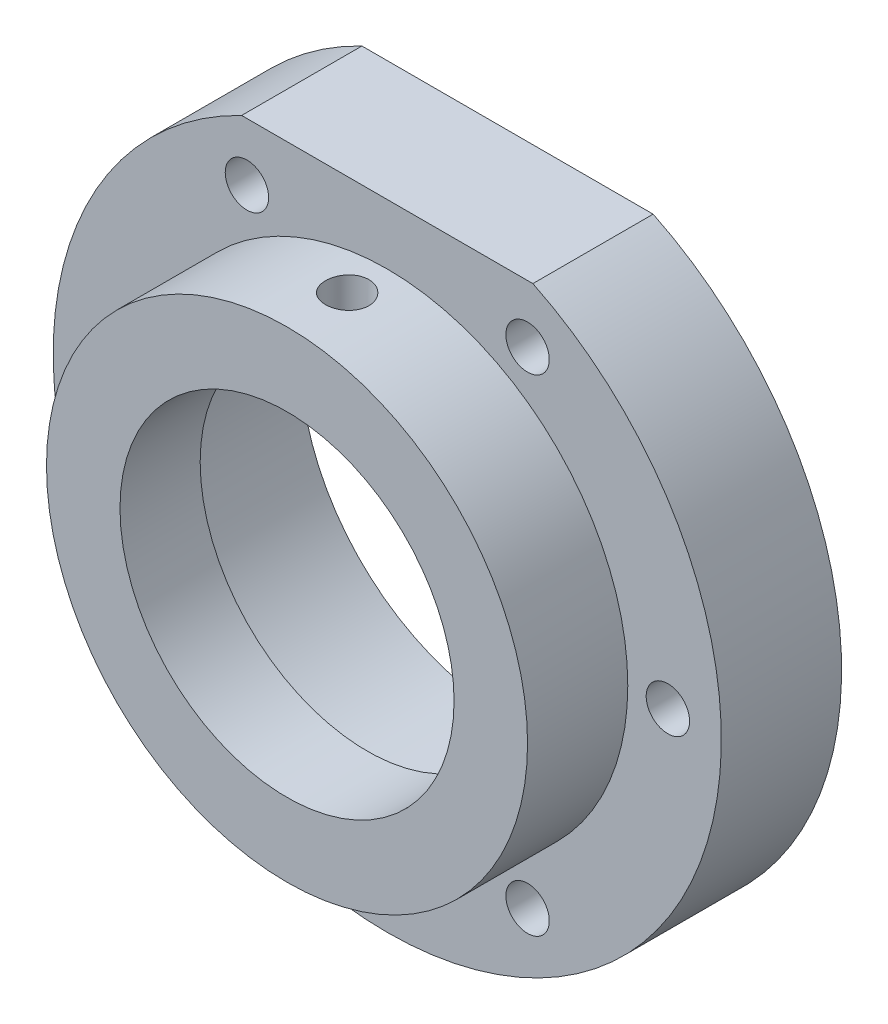
SolidWorks part; units mm, degrees
ref_plane "Alzado" through (0, 0, 0) normal (0, 0, 1) x (1, 0, 0)
ref_plane "Planta" through (0, 0, 0) normal (0, 1, 0) x (1, 0, 0)
ref_plane "Vista lateral" through (0, 0, 0) normal (1, 0, 0) x (0, 0, -1)
sketch "Croquis1" plane through (0, 0, 0) normal (0, 0, 1) x (1, 0, 0)
  line L0 (-21.7945, 45) -> (21.7945, 45)
  arc A0 (-21.7945, 45) -> (21.7945, 45) centre (0, 0) ccw
  dimension "D1" = 100
  dimension "D2" = 45
extrude "Saliente-Extruir1" add sketch "Croquis1" along normal blind 18
sketch "Croquis2" plane through (0, 0, 18) normal (0, 0, 1) x (1, 0, 0)
  circle A0 centre (0, 0) radius 36
  dimension "D1" = 72
extrude "Saliente-Extruir2" add sketch "Croquis2" along normal blind 15
sketch "Croquis3" plane through (0, 0, 0) normal (0, 0, -1) x (-1, 0, 0)
  circle A0 centre (0, 0) radius 31
  dimension "D1" = 62
extrude "Cortar-Extruir1" cut sketch "Croquis3" against normal blind 21
sketch "Croquis4" plane through (0, 0, 21) normal (0, 0, -1) x (-1, 0, 0)
  circle A0 centre (0, 0) radius 25
  dimension "D1" = 50
extrude "Cortar-Extruir2" cut sketch "Croquis4" against normal blind 21
sketch "Croquis5" plane through (0, 0, 0) normal (0, 0, -1) x (-1, 0, 0)
  line L0 (-42, 0) -> (0, 0) construction
  circle A0 centre (-42, 0) radius 3.25
  dimension "D2" = 6.5
  dimension "D1" = 42
extrude "Cortar-Extruir3" cut sketch "Croquis5" against normal blind 21
pattern_circular "MatrizC1" count 6 over 360 about axis through (0, 0, 0) along (0, 0, 1) of "Cortar-Extruir3"
sketch "Croquis6" plane through (0, 0, 0) normal (0, 0, -1) x (-1, 0, 0)
  circle A0 centre (-21, 36.3731) radius 5
  dimension "D1" = 10
extrude "Cortar-Extruir4" cut sketch "Croquis6" against normal blind 6
pattern_circular "MatrizC2" count 6 over 360 about axis through (0, 0, 0) along (0, 0, 1) of "Cortar-Extruir4"
sketch "Croquis7" plane through (0, 45, 0) normal (0, 1, 0) x (1, 0, 0)
  line L0 (21.7945, 0) -> (-21.7945, 0) construction
  circle A0 centre (0, -24) radius 3.25
  dimension "D1" = 6.5
  dimension "D2" = 24
extrude "Cortar-Extruir5" cut sketch "Croquis7" against normal blind 27
